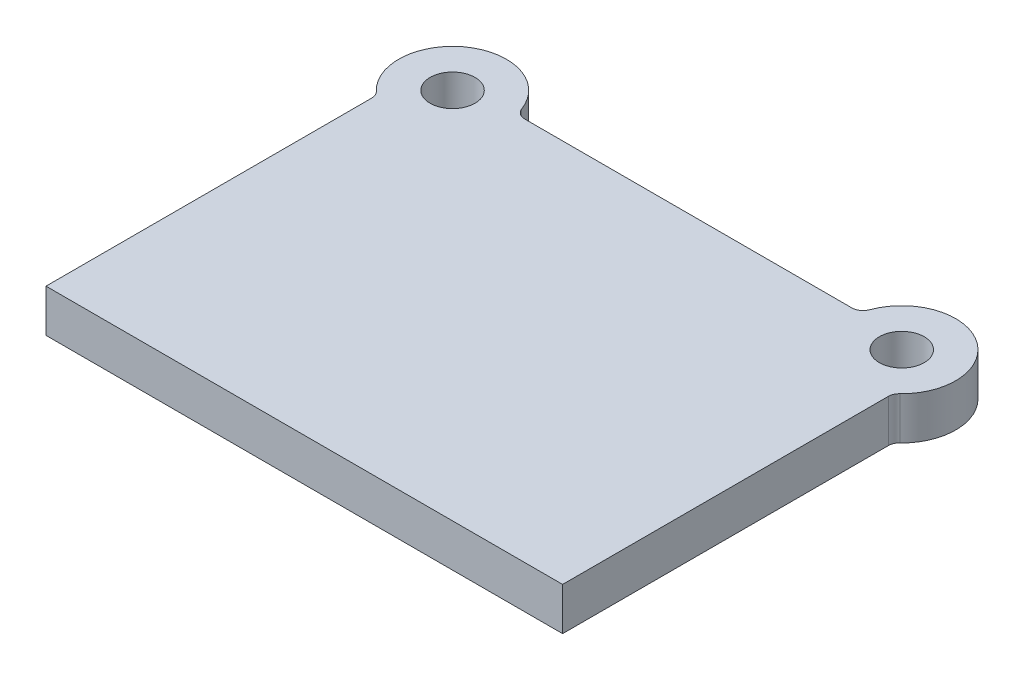
SolidWorks part; units mm, degrees
ref_plane "Front Plane" through (0, 0, 0) normal (0, 0, 1) x (1, 0, 0)
ref_plane "Top Plane" through (0, 0, 0) normal (0, 1, 0) x (1, 0, 0)
ref_plane "Right Plane" through (0, 0, 0) normal (1, 0, 0) x (0, 0, -1)
sketch "Sketch1" plane through (0, 0, 0) normal (0, 1, 0) x (1, 0, 0)
  line L0 (230, 0) -> (-230, 0)
  line L1 (-230, 0) -> (-230, 294.53)
  line L2 (0, 0) -> (0, 342) construction
  line L3 (153.0532, 342) -> (-153.0532, 342)
  line L4 (230, 0) -> (230, 294.53)
  arc A0 (-153.0532, 342) -> (-230, 294.53) centre (-200, 332) ccw
  circle A1 centre (-200, 332) radius 20
  circle A2 centre (200, 332) radius 20
  arc A3 (153.0532, 342) -> (230, 294.53) centre (200, 332) cw
  point P9 (-299.0199, 332)
  point P10 (-332.7329, 273.6073)
  point P11 (-240.6272, 365.713)
  point P12 (0, 342)
  dimension "D2" = 40
  dimension "D3" = 96
  dimension "D1" = 332
  dimension "D4" = 342
  dimension "D5" = 460
  dimension "D6" = 400
extrude "Boss-Extrude1" add sketch "Sketch1" along normal blind 38
fillet "Fillet1" radius 10 4 edges at (-230, 19, -294.53) (230, 19, -294.53) (-153.0532, 19, -342) (153.0532, 19, -342)
